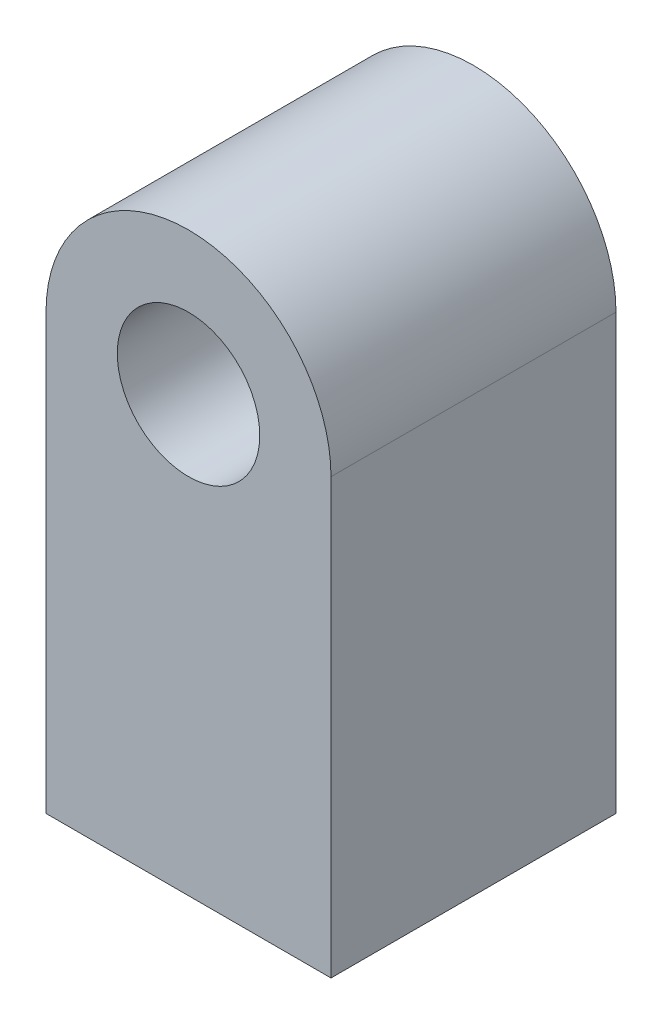
SolidWorks part; units mm, degrees
ref_plane "Front Plane" through (0, 0, 0) normal (0, 0, 1) x (1, 0, 0)
ref_plane "Top Plane" through (0, 0, 0) normal (0, 1, 0) x (1, 0, 0)
ref_plane "Right Plane" through (0, 0, 0) normal (1, 0, 0) x (0, 0, -1)
sketch "sketch1_link1" plane through (0, 0, 0) normal (0, 0, 1) x (1, 0, 0)
  line L0 (-40, 0) -> (-40, 121.875)
  line L1 (40, 0) -> (40, 121.875)
  line L2 (0, 0) -> (-40, 0)
  line L3 (0, 0) -> (40, 0)
  arc A0 (-40, 121.875) -> (40, 121.875) centre (0, 121.875) cw
  circle A1 centre (0, 121.875) radius 20
  dimension "D3" = 40
  dimension "D1" = 80
  dimension "D2" = 121.875
extrude "Boss-Extrude1" add sketch "sketch1_link1" along normal mid plane 80
sketch "sketch2_link1" plane through (0, 0, 0) normal (0, 1, 0) x (1, 0, 0)
  circle A0 centre (0, 0) radius 20
  dimension "D1" = 40
extrude "Cut-Extrude1" cut sketch "sketch2_link1" along normal blind 40
equation "\"D2@sketch1_link1\"=0.1625*0.75m"
